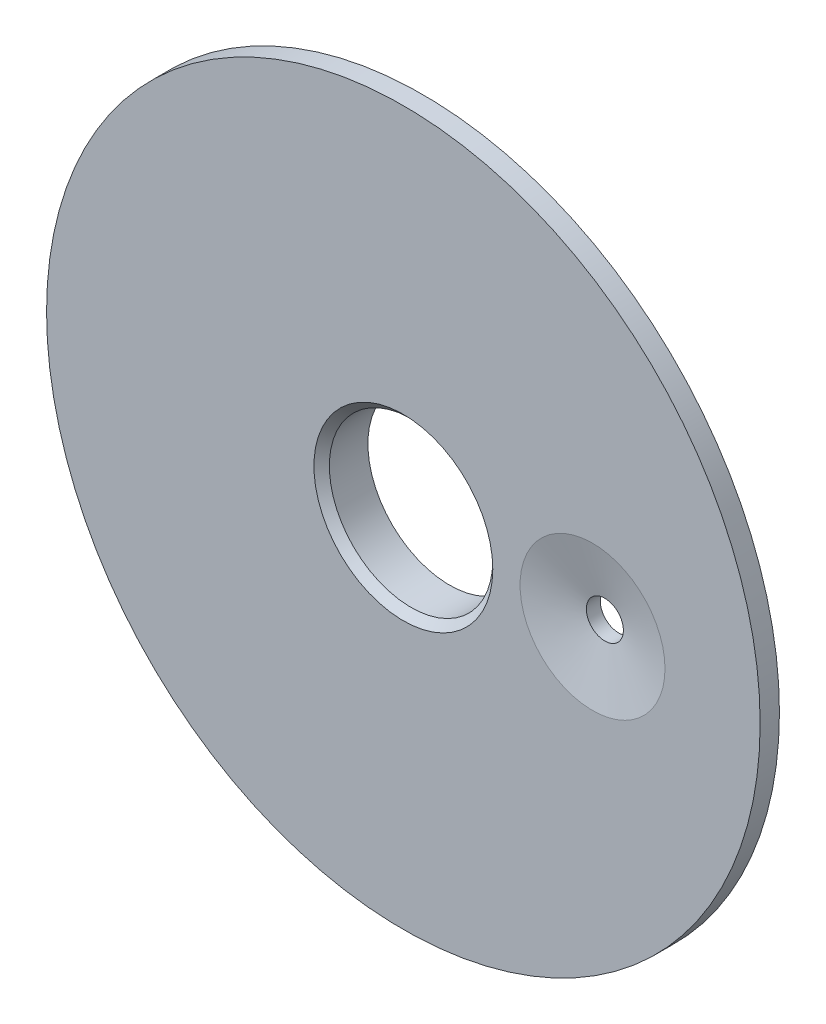
SolidWorks part; units mm, degrees
material "有机玻璃 (TM) GS 丙烯酸铸钣"
ref_plane "前视基准面" through (0, 0, 0) normal (0, 0, 1) x (1, 0, 0)
ref_plane "上视基准面" through (0, 0, 0) normal (0, 1, 0) x (1, 0, 0)
ref_plane "右视基准面" through (0, 0, 0) normal (1, 0, 0) x (0, 0, -1)
sketch "草图1" plane through (0, 0, 0) normal (0, 0, 1) x (1, 0, 0)
  circle A0 centre (91.999, 78.41) radius 23.14
sketch "草图2" plane through (0, 0, 0) normal (0, 0, 1) x (1, 0, 0)
  circle A0 centre (91.999, 78.41) radius 20.2
sketch "草图3" plane through (0, 0, 0) normal (0, 0, 1) x (1, 0, 0)
  line L0 (101.346, 82.55) -> (101.727, 82.931)
  line L1 (101.727, 82.931) -> (106.807, 82.931)
  line L2 (106.807, 82.931) -> (107.315, 82.423)
  line L3 (107.315, 74.803) -> (107.315, 82.423)
  line L4 (106.68, 74.168) -> (107.315, 74.803)
  line L5 (101.6, 74.168) -> (106.68, 74.168)
  line L6 (101.346, 74.422) -> (101.6, 74.168)
  line L7 (101.346, 74.422) -> (101.346, 82.55)
  line L8 (84.201, 85.471) -> (84.201, 87.122)
  line L9 (83.566, 87.757) -> (84.201, 87.122)
  line L10 (79.121, 87.757) -> (83.566, 87.757)
  line L11 (78.74, 88.138) -> (79.121, 87.757)
  line L12 (78.74, 88.138) -> (78.74, 90.551)
  line L13 (78.74, 90.551) -> (79.248, 91.059)
  line L14 (79.248, 91.059) -> (79.248, 93.599)
  line L15 (79.248, 93.599) -> (79.629, 93.98)
  line L16 (79.629, 93.98) -> (84.074, 93.98)
  line L17 (84.074, 93.98) -> (84.328, 94.234)
  line L18 (84.328, 94.234) -> (84.328, 97.6677)
  line L19 (99.695, 96.266) -> (99.695, 97.6584)
  line L20 (99.695, 96.266) -> (99.949, 96.012)
  line L21 (99.949, 96.012) -> (101.219, 96.012)
  line L22 (101.219, 96.012) -> (101.6, 95.631)
  line L23 (101.6, 94.234) -> (101.6, 95.631)
  line L24 (101.6, 94.234) -> (101.854, 93.98)
  line L25 (101.854, 93.98) -> (104.14, 93.98)
  line L26 (104.14, 93.98) -> (104.648, 93.472)
  line L27 (104.648, 87.376) -> (104.648, 93.472)
  line L28 (104.14, 86.868) -> (104.648, 87.376)
  line L29 (99.695, 86.868) -> (104.14, 86.868)
  line L30 (99.568, 86.741) -> (99.695, 86.868)
  line L31 (99.568, 85.725) -> (99.568, 86.741)
  line L32 (84.201, 85.471) -> (84.455, 85.217)
  line L33 (99.568, 85.471) -> (99.568, 85.725)
  line L34 (99.314, 85.217) -> (99.568, 85.471)
  line L35 (97.282, 85.217) -> (99.314, 85.217)
  line L36 (96.7627, 84.6977) -> (97.282, 85.217)
  line L39 (86.233, 85.217) -> (86.7523, 84.6978)
  line L40 (84.455, 85.217) -> (86.233, 85.217)
  line L41 (86.7523, 84.6978) -> (96.7627, 84.6977)
  arc A82 (99.695, 97.6584) -> (84.328, 97.6677) centre (91.9998, 78.4096) ccw
extrude "凸台-拉伸1" add sketch "草图1" along normal blind 1.25
extrude "凸台-拉伸2" add sketch "草图2" against normal blind 1.75
extrude "切除-拉伸1" cut sketch "草图3" against normal up to surface (1.75 mm away) from surface at 0 contours L19 A82 L18 L17 L16 L15 L14 L13 L12 L11 L10 L9 L8 L32 L40 L39 L41 L36 L35 L34 L33 L31 L30 L29 L28 L27 L26 L25 L24 L23 L22 L21 L20 up to face at (112.199, 78.41, -1.75) starting at face at (112.199, 78.41, 0)
sketch "草图5" plane through (0, 0, 0) normal (0, 0, 1) x (1, 0, 0)
  circle A0 centre (104.267, 78.41) radius 1.2
  circle A3 centre (91.999, 78.41) radius 5.3
extrude "切除-拉伸2" cut sketch "草图5" against normal up to next (1.75 mm away) from surface at 1.25 starting at face at (115.139, 78.41, 1.25)
chamfer "倒角1" distance 3.5 distance2 0.8 1 edges at (105.467, 78.41, 1.25)
chamfer "倒角2" distance 0.5 angle 45 1 edges at (97.299, 78.41, 1.25)
sketch "草图6" plane through (0, 0, 0) normal (0, 0, 1) x (1, 0, 0)
  line L0 (101.727, 82.931) -> (101.346, 82.55)
  line L1 (101.346, 82.55) -> (101.346, 74.422)
  line L2 (101.346, 74.422) -> (101.6, 74.168)
  line L3 (101.6, 74.168) -> (106.68, 74.168)
  line L4 (106.68, 74.168) -> (107.315, 74.803)
  line L5 (107.315, 74.803) -> (107.315, 82.423)
  line L6 (107.315, 82.423) -> (106.807, 82.931)
  line L7 (106.807, 82.931) -> (101.727, 82.931)
extrude "切除-拉伸3" cut sketch "草图6" along normal blind 1.3 from surface at -1.75 starting at face at (105.467, 78.41, -1.75)
